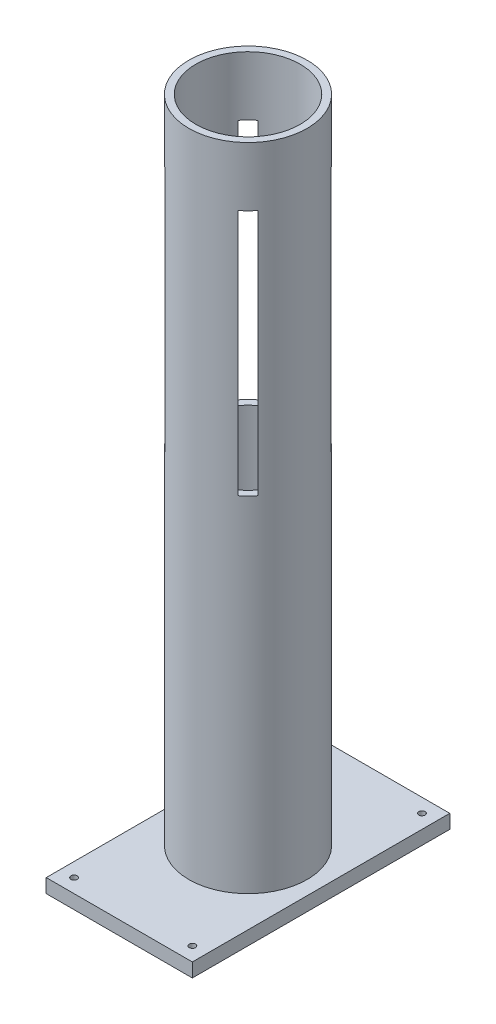
SolidWorks part; units mm, degrees
ref_plane "Front Plane" through (0, 0, 0) normal (0, 0, 1) x (1, 0, 0)
ref_plane "Top Plane" through (0, 0, 0) normal (0, 1, 0) x (1, 0, 0)
ref_plane "Right Plane" through (0, 0, 0) normal (1, 0, 0) x (0, 0, -1)
sketch "Sketch1" plane through (0, 0, 0) normal (0, 1, 0) x (1, 0, 0)
  line L1 (-105, -185) -> (105, -185)
  line L2 (-105, -185) -> (-105, 185)
  line L3 (-105, 185) -> (105, 185)
  line L4 (105, -185) -> (105, 185)
  line L5 (-105, -185) -> (105, 185) construction
  line L6 (-105, 185) -> (105, -185) construction
  point P0 (0, 0)
  dimension "D1" = 370
  dimension "D2" = 210
extrude "Boss-Extrude1" add sketch "Sketch1" along normal blind 20
sketch "Sketch2" plane through (0, 20, 0) normal (0, 1, 0) x (1, 0, 0)
  circle A0 centre (0, 0) radius 85
  dimension "D1" = 170
extrude "Boss-Extrude2" add sketch "Sketch2" along normal blind 935
sketch "Sketch3" plane through (0, 955, 0) normal (0, 1, 0) x (1, 0, 0)
  circle A0 centre (0, 0) radius 75
  dimension "D1" = 150
extrude "Cut-Extrude1" cut sketch "Sketch3" against normal through all
sketch "Sketch4" plane through (0, 0, 0) normal (0, -1, 0) x (1, 0, 0)
  line L1 (-105, -185) -> (-105, 185) construction
  line L2 (-105, 185) -> (105, 185) construction
  line L3 (105, 185) -> (105, -185) construction
  line L4 (105, -185) -> (-105, -185) construction
  circle A0 centre (-85, 165) radius 4.5
  circle A1 centre (85, 165) radius 4.5
  circle A2 centre (85, -165) radius 4.5
  circle A3 centre (-85, -165) radius 4.5
  dimension "D1" = 9
  dimension "D2" = 9
  dimension "D3" = 9
  dimension "D4" = 9
  dimension "D5" = 20
  dimension "D6" = 20
  dimension "D7" = 20
  dimension "D8" = 20
extrude "Cut-Extrude2" cut sketch "Sketch4" against normal through all
sketch "Sketch5" plane through (0, 0, 0) normal (0, -1, 0) x (1, 0, 0)
  circle A0 centre (-85, 165) radius 9
  circle A1 centre (85, 165) radius 9
  circle A2 centre (85, -165) radius 9
  circle A3 centre (-85, -165) radius 9
  dimension "D1" = 18
  dimension "D2" = 18
  dimension "D3" = 18
  dimension "D4" = 18
extrude "Cut-Extrude3" cut sketch "Sketch5" against normal blind 8.8
sketch "Sketch6" plane through (0, 955, 0) normal (0, 1, 0) x (1, 0, 0)
  line L0 (0, 0) -> (0, 85) construction
  line L1 (0, 0) -> (60.1041, 60.1041) construction
  line L2 (0, 0) -> (60.1041, -60.1041) construction
  line L3 (0, 0) -> (-60.1041, -60.1041) construction
  line L4 (0, 0) -> (-60.1041, 60.1041) construction
  circle A0 centre (0, 0) radius 85 construction
  circle A2 centre (0, 0) radius 85 construction
  dimension "D1" = 45
  dimension "D2" = 90
  dimension "D3" = 90
  dimension "D4" = 90
ref_plane "Plane1" through (60.1041, 0, 60.1041) normal (0.7071, 0, 0.7071) x (0.7071, 0, -0.7071)
sketch "Sketch7" plane through (60.1041, 0, 60.1041) normal (0.7071, 0, 0.7071) x (0.7071, 0, -0.7071)
  line L0 (0, 870) -> (0, 515) construction
  line L1 (-56.5685, 20) -> (205.061, 20) construction
  line L2 (-10, 870) -> (-10, 515)
  line L3 (10, 870) -> (10, 515)
  line L4 (-10, 870) -> (10, 870)
  line L5 (-10, 515) -> (10, 515)
  dimension "D1" = 355
  dimension "D2" = 495
  dimension "D3" = 10
  dimension "D4" = 10
extrude "Cut-Extrude4" cut sketch "Sketch7" against normal through all
ref_plane "Plane2" through (60.1041, 0, -60.1041) normal (0.7071, 0, -0.7071) x (-0.7071, 0, -0.7071)
sketch "Sketch8" plane through (60.1041, 0, -60.1041) normal (0.7071, 0, -0.7071) x (-0.7071, 0, -0.7071)
  line L0 (0, 870) -> (0, 515) construction
  line L1 (-10, 870) -> (-10, 515)
  line L2 (10, 870) -> (10, 515)
  line L3 (-10, 870) -> (10, 870)
  line L4 (-10, 515) -> (10, 515)
  dimension "D1" = 355
  dimension "D2" = 495
  dimension "D3" = 10
  dimension "D4" = 10
extrude "Cut-Extrude5" cut sketch "Sketch8" against normal through all
